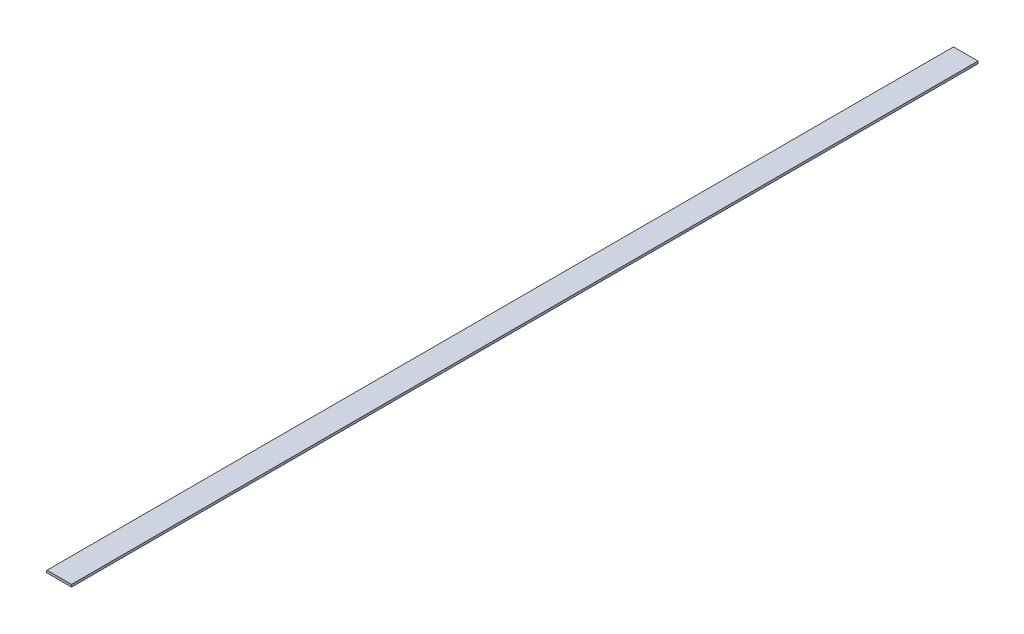
SolidWorks part; units mm, degrees
ref_plane "Front Plane" through (0, 0, 0) normal (0, 0, 1) x (1, 0, 0)
ref_plane "Top Plane" through (0, 0, 0) normal (0, 1, 0) x (1, 0, 0)
ref_plane "Right Plane" through (0, 0, 0) normal (1, 0, 0) x (0, 0, -1)
sketch "Sketch1" plane through (0, 0, 0) normal (0, 0, 1) x (1, 0, 0)
  line L0 (0, 0) -> (25.4, 0)
  line L1 (25.4, 0) -> (25.4, 2.3622)
  line L2 (25.4, 2.3622) -> (0.9785, 2.3622)
  line L3 (0.9785, 2.3622) -> (0, 0)
  dimension "D1" = 67.5
  dimension "D2" = 25.4
  dimension "D3" = 2.3622
extrude "Boss-Extrude1" add sketch "Sketch1" along normal blind 901.7
